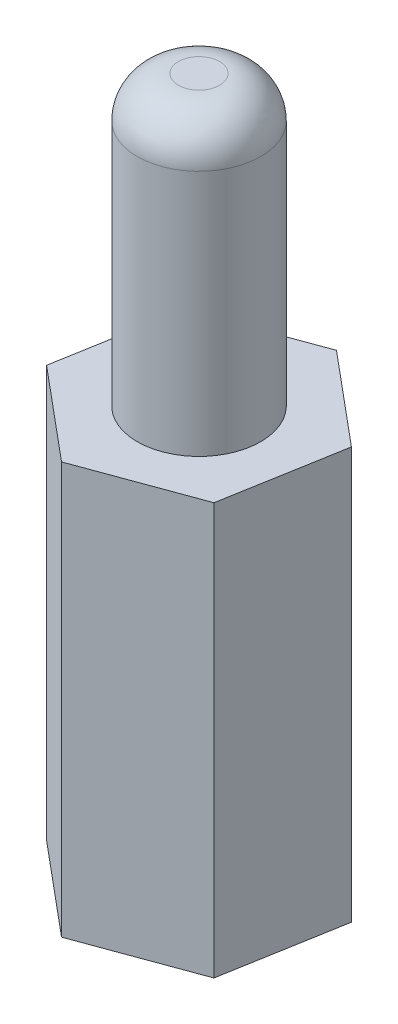
SolidWorks part; units mm, degrees
ref_plane "Front Plane" through (0, 0, 0) normal (0, 0, 1) x (1, 0, 0)
ref_plane "Top Plane" through (0, 0, 0) normal (0, 1, 0) x (1, 0, 0)
ref_plane "Right Plane" through (0, 0, 0) normal (1, 0, 0) x (0, 0, -1)
sketch "Sketch1" plane through (0, 0, 0) normal (0, 1, 0) x (1, 0, 0)
  line L1 (2.2148, -1.8515) -> (2.7108, 0.9924)
  line L2 (2.7108, 0.9924) -> (0.496, 2.8438)
  line L3 (0.496, 2.8438) -> (-2.2148, 1.8515)
  line L4 (-2.2148, 1.8515) -> (-2.7108, -0.9924)
  line L5 (-2.7108, -0.9924) -> (-0.496, -2.8438)
  line L6 (-0.496, -2.8438) -> (2.2148, -1.8515)
  circle A0 centre (0, 0) radius 2.5 construction
  dimension "D1" = 5
extrude "Boss-Extrude1" add sketch "Sketch1" along normal blind 10
sketch "Sketch2" plane through (0, 10, 0) normal (0, 1, 0) x (1, 0, 0)
  circle A0 centre (0, 0) radius 1.5
  dimension "D1" = 3
extrude "Boss-Extrude2" add sketch "Sketch2" along normal blind 7
sketch "Sketch3" plane through (0, 0, 0) normal (0, -1, 0) x (1, 0, 0)
  circle A0 centre (0, 0) radius 1.5
extrude "Cut-Extrude1" cut sketch "Sketch3" against normal blind 7
fillet "Fillet1" radius 1 1 edges at (0, 17, 1.5)
